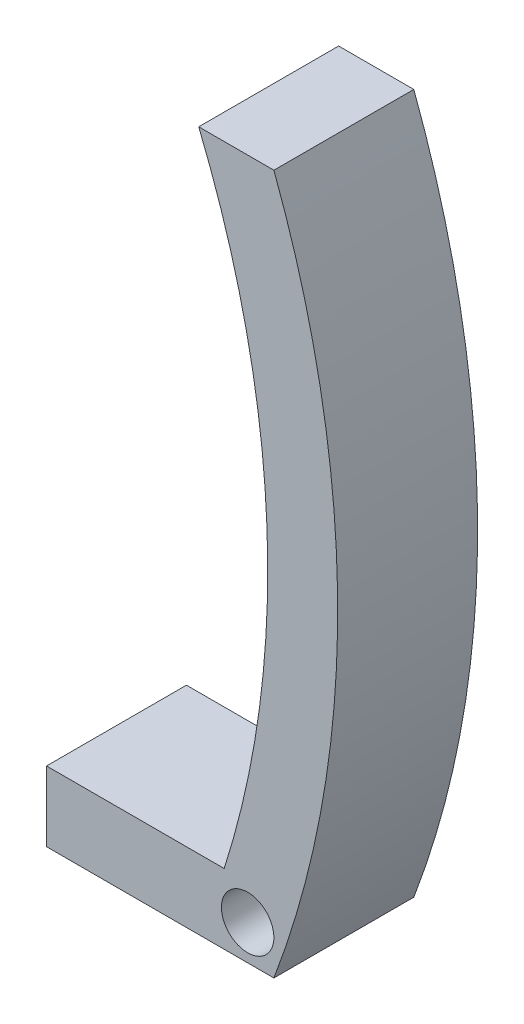
SolidWorks part; units mm, degrees
material "ABS"
ref_plane "Front" through (0, 0, 0) normal (0, 0, 1) x (1, 0, 0)
ref_plane "Top" through (0, 0, 0) normal (0, 1, 0) x (1, 0, 0)
ref_plane "Right" through (0, 0, 0) normal (1, 0, 0) x (0, 0, -1)
sketch "Sketch1" plane through (0, 0, 0) normal (0, 0, 1) x (1, 0, 0)
  line L0 (0, 0) -> (16.51, 0)
  line L1 (0, 0) -> (0, 5.08)
  line L2 (0, 5.08) -> (12.9005, 5.08)
  line L3 (16.51, 50.8) -> (11.0506, 50.8)
  arc A0 (16.51, 0) -> (16.51, 50.8) centre (-50.8, 25.4) ccw
  arc A1 (12.9005, 5.08) -> (11.0506, 50.8) centre (-50.8, 25.4) ccw
  dimension "D1" = 16.51
  dimension "D2" = 50.8
  dimension "D5" = 5.08
  dimension "D3" = 5.08
  dimension "D4" = 50.8
extrude "Boss-Extrude1" add sketch "Sketch1" along normal blind 10.16
sketch "Sketch2" plane through (0, 0, 10.16) normal (0, 0, 1) x (1, 0, 0)
  line L0 (0, 5.08) -> (0, 0) construction
  circle A0 centre (14.605, 2.54) radius 1.905
  point P2 (0, 2.54)
  dimension "D1" = 3.81
  dimension "D2" = 14.605
extrude "Cut-Extrude1" cut sketch "Sketch2" against normal through all and the other way through all
